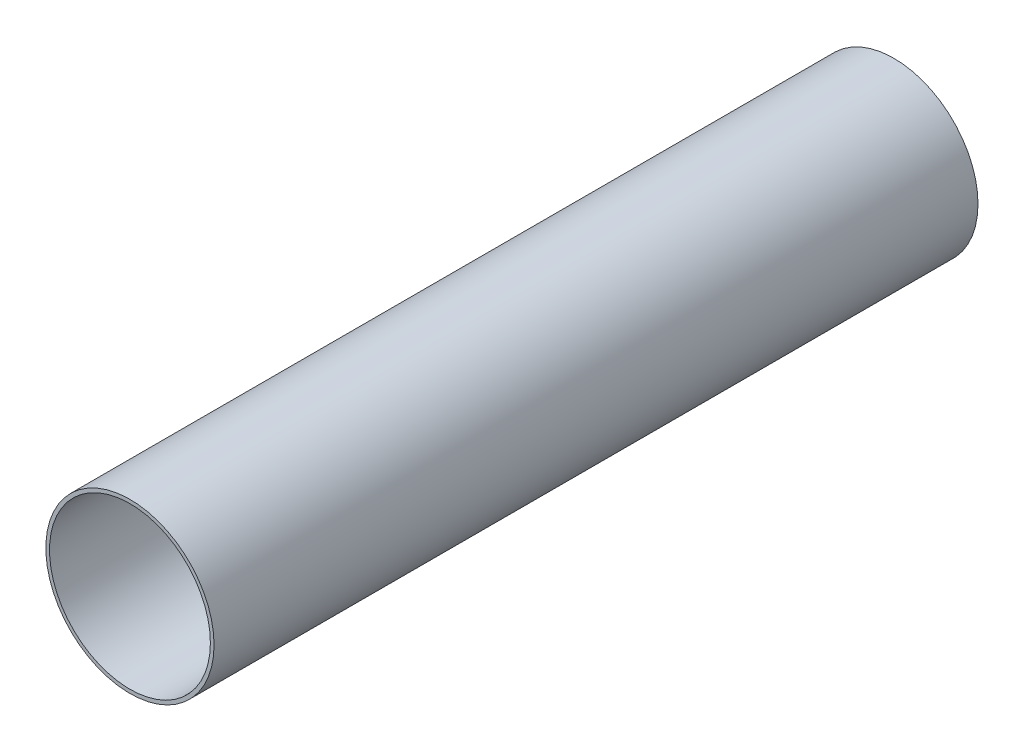
SolidWorks part; units mm, degrees
ref_plane "Front Plane" through (0, 0, 0) normal (0, 0, 1) x (1, 0, 0)
ref_plane "Top Plane" through (0, 0, 0) normal (0, 1, 0) x (1, 0, 0)
ref_plane "Right Plane" through (0, 0, 0) normal (1, 0, 0) x (0, 0, -1)
sketch "Sketch1" plane through (0, 0, 0) normal (0, 0, 1) x (1, 0, 0)
  circle A0 centre (0, 0) radius 28.625
  dimension "D1" = 57.25
extrude "Boss-Extrude1" add sketch "Sketch1" against normal blind 260
sketch "Sketch2" plane through (0, 0, 0) normal (0, 0, 1) x (1, 0, 0)
  circle A0 centre (0, 0) radius 27.375
  dimension "D1" = 54.75
extrude "Cut-Extrude1" cut sketch "Sketch2" against normal up to next
